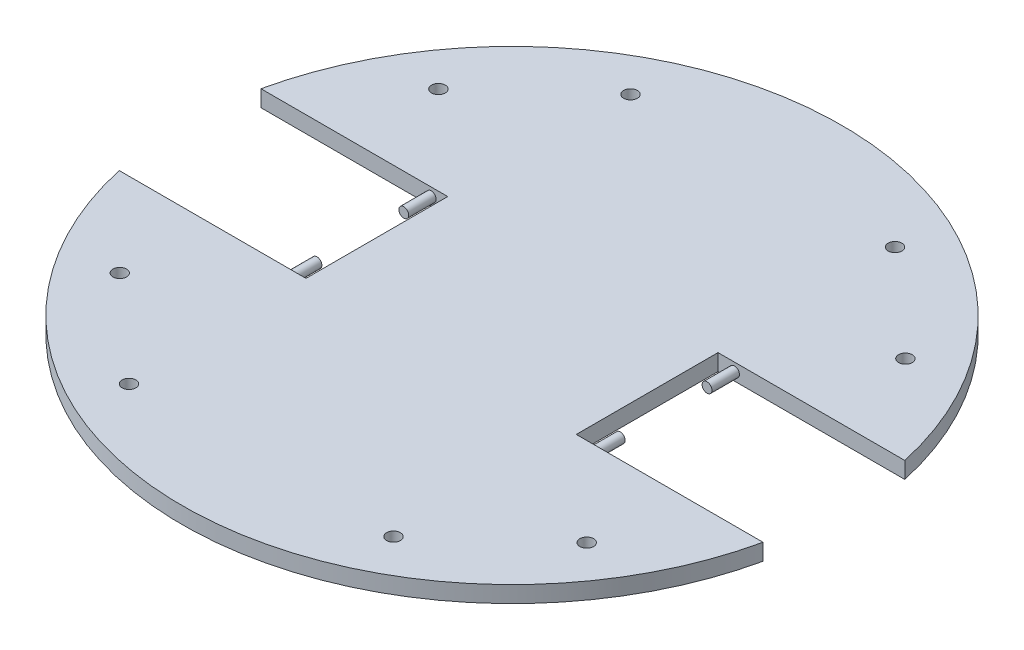
SolidWorks part; units mm, degrees
ref_plane "Front Plane" through (0, 0, 0) normal (0, 0, 1) x (1, 0, 0)
ref_plane "Top Plane" through (0, 0, 0) normal (0, 1, 0) x (1, 0, 0)
ref_plane "Right Plane" through (0, 0, 0) normal (1, 0, 0) x (0, 0, -1)
sketch "Sketch1" plane through (0, 0, 0) normal (0, 1, 0) x (1, 0, 0)
  circle A0 centre (0, 0) radius 60
  dimension "D1" = 120
extrude "Boss-Extrude1" add sketch "Sketch1" along normal blind 3
sketch "Sketch2" plane through (0, 3, 0) normal (0, 1, 0) x (1, 0, 0)
  line L0 (0, 60) -> (0, -60) construction
  line L1 (-60, 0) -> (60, 0) construction
  line L2 (-42.3936, -29.0021) -> (42.6064, -29.0021) construction
  line L3 (-42.3936, 29.0021) -> (42.6064, 29.0021) construction
  circle A0 centre (0, 0) radius 60 construction
  circle A1 centre (-42.3936, 29.0021) radius 1.25
  circle A2 centre (42.6064, 29.0021) radius 1.25
  circle A3 centre (42.6064, -29.0021) radius 1.25
  circle A4 centre (-42.3936, -29.0021) radius 1.25
  circle A5 centre (0, 0) radius 51.6037 construction
  circle A6 centre (-24.0731, 45.6446) radius 1.25
  circle A7 centre (24.0731, 45.6446) radius 1.25
  circle A8 centre (24.0731, -45.6446) radius 1.25
  circle A9 centre (-24.0731, -45.6446) radius 1.25
  dimension "D2" = 2.5
  dimension "D3" = 2.5
  dimension "D4" = 2.5
  dimension "D1" = 85
extrude "Cut-Extrude1" cut sketch "Sketch2" against normal through all
sketch "Sketch4" plane through (0, 3, 0) normal (0, 1, 0) x (1, 0, 0)
  line L0 (0, 0) -> (60, 0) construction
  line L1 (24.6, 12.9) -> (58.5968, 12.9)
  line L2 (24.6, 12.9) -> (24.6, -12.9)
  line L3 (60, 0) -> (24.6, 0)
  line L4 (0, 60) -> (0, -60) construction
  line L5 (24.6, -12.9) -> (58.5968, -12.9)
  line L6 (-24.6, -12.9) -> (-58.5968, -12.9)
  line L7 (-24.6, 12.9) -> (-24.6, -12.9)
  line L8 (-24.6, 12.9) -> (-58.5968, 12.9)
  circle A0 centre (0, 0) radius 60 construction
  circle M13 centre (0, 0) radius 60
  dimension "D1" = 12.9
  dimension "D2" = 35.4
extrude "Cut-Extrude9" cut sketch "Sketch4" against normal through all contours L7 L8 L6 M13 | L3 L1 L2 M13 | L2 L5 L3 M13
sketch "Sketch5" plane through (0, 0, -12.9) normal (0, 0, 1) x (1, 0, 0)
  line L0 (58.5968, 1.5) -> (24.6, 1.5) construction
  line L1 (58.5968, 0) -> (58.5968, 3) construction
  line L2 (24.6, 0) -> (24.6, 3) construction
  line L3 (27.6, 3) -> (27.6, 0) construction
  line L4 (24.6, 3) -> (58.5968, 3) construction
  line L5 (24.6, 0) -> (58.5968, 0) construction
  circle A0 centre (27.6, 1.5) radius 0.9
  dimension "D2" = 1.8
  dimension "D1" = 3
extrude "Boss-Extrude2" add sketch "Sketch5" along normal blind 5
sketch "Sketch7" plane through (0, 0, 12.9) normal (0, 0, -1) x (-1, 0, 0)
  line L0 (-24.6, 1.5) -> (-58.5968, 1.5) construction
  line L1 (-24.6, 0) -> (-24.6, 3) construction
  line L2 (-58.5968, 0) -> (-58.5968, 3) construction
  line L3 (-27.6, 0) -> (-27.6, 3) construction
  line L4 (-24.6, 0) -> (-58.5968, 0) construction
  line L5 (-24.6, 3) -> (-58.5968, 3) construction
  circle A0 centre (-27.6, 1.5) radius 0.9
  dimension "D2" = 1.8
  dimension "D1" = 3
extrude "Boss-Extrude3" add sketch "Sketch7" along normal blind 5
sketch "Sketch8" plane through (0, 0, -12.9) normal (0, 0, 1) x (1, 0, 0)
  line L0 (-24.6, 1.5) -> (-58.5968, 1.5) construction
  line L1 (-24.6, 0) -> (-24.6, 3) construction
  line L2 (-58.5968, 0) -> (-58.5968, 3) construction
  line L3 (-27.6, 3) -> (-27.6, 0) construction
  line L4 (-24.6, 3) -> (-58.5968, 3) construction
  line L5 (-24.6, 0) -> (-58.5968, 0) construction
  circle A0 centre (-27.6, 1.5) radius 0.9
  dimension "D2" = 1.8
  dimension "D1" = 3
extrude "Boss-Extrude4" add sketch "Sketch8" along normal blind 5
sketch "Sketch9" plane through (0, 0, 12.9) normal (0, 0, -1) x (-1, 0, 0)
  line L0 (24.6, 1.5) -> (58.5968, 1.5) construction
  line L1 (24.6, 0) -> (24.6, 3) construction
  line L2 (58.5968, 0) -> (58.5968, 3) construction
  line L3 (28.2422, 0) -> (27.6, 0) construction
  line L4 (24.6, 0) -> (58.5968, 0) construction
  line L5 (27.6, 0) -> (27.6, 3) construction
  line L6 (24.6, 3) -> (58.5968, 3) construction
  circle A0 centre (27.6, 1.5) radius 0.9
  dimension "D2" = 1.8
  dimension "D1" = 3
extrude "Boss-Extrude5" add sketch "Sketch9" along normal blind 5
